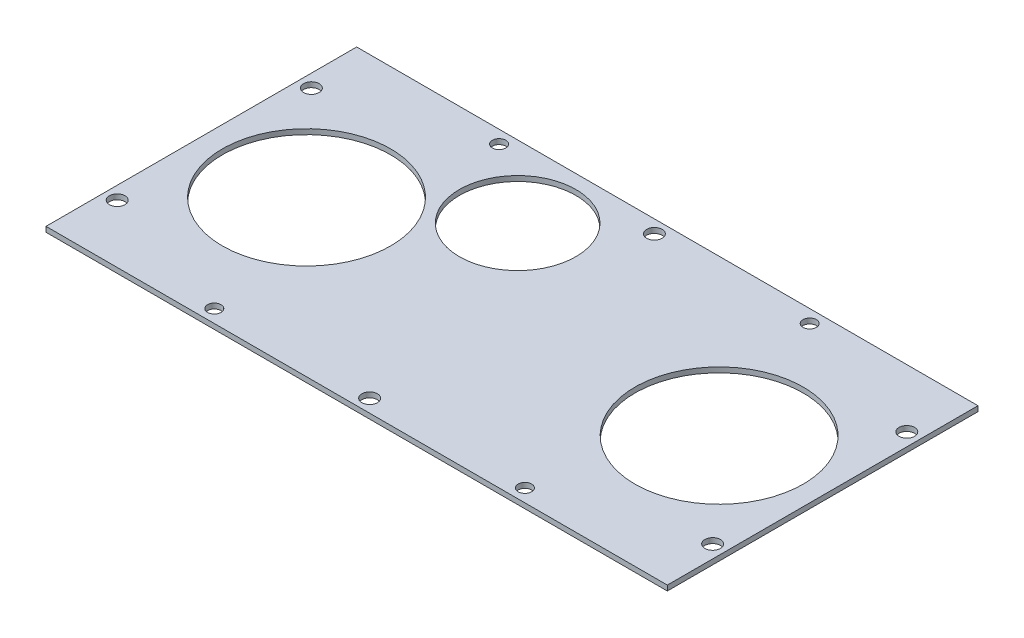
SolidWorks part; units mm, degrees
ref_plane "Front Plane" through (0, 0, 0) normal (0, 0, 1) x (1, 0, 0)
ref_plane "Top Plane" through (0, 0, 0) normal (0, 1, 0) x (1, 0, 0)
ref_plane "Right Plane" through (0, 0, 0) normal (1, 0, 0) x (0, 0, -1)
sketch "Sketch1" plane through (0, 0, 0) normal (0, 1, 0) x (1, 0, 0)
  line L1 (-152.4, 76.2) -> (152.4, 76.2)
  line L2 (-152.4, 76.2) -> (-152.4, -76.2)
  line L3 (-152.4, -76.2) -> (152.4, -76.2)
  line L4 (152.4, 76.2) -> (152.4, -76.2)
  circle A1 centre (-100.8031, 0) radius 41.275
  circle A2 centre (101.6, 0) radius 41.275
  circle A3 centre (146.05, 47.625) radius 3.81
  circle A4 centre (76.2, 69.85) radius 3.302
  circle A5 centre (-146.05, 47.625) radius 3.81
  circle A6 centre (-146.05, -47.625) radius 3.81
  circle A7 centre (-76.2, -69.85) radius 3.302
  circle A8 centre (76.2, -69.85) radius 3.302
  circle A9 centre (146.05, -47.625) radius 3.81
  circle A10 centre (0, -69.85) radius 3.81
  circle A11 centre (-76.2, 69.85) radius 3.302
  circle A12 centre (0, 69.85) radius 3.81
  dimension "D2" = 82.55
  dimension "D3" = 82.55
  dimension "D4" = 7.62
  dimension "D7" = 7.62
  dimension "D8" = 6.604
  dimension "D9" = 6.604
  dimension "D10" = 7.62
  dimension "D11" = 7.62
  dimension "D12" = 6.604
  dimension "D32" = 7.62
  dimension "D35" = 6.604
  dimension "D38" = 7.62
  dimension "D5" = 28.575
  dimension "D6" = 6.35
  dimension "D13" = 28.575
  dimension "D14" = 6.35
  dimension "D15" = 6.35
  dimension "D16" = 28.575
  dimension "D17" = 6.35
  dimension "D18" = 6.35
  dimension "D19" = 6.35
  dimension "D20" = 28.575
  dimension "D21" = 304.8
  dimension "D22" = 152.4
  dimension "D23" = 76.2
  dimension "D24" = 76.2
  dimension "D25" = 76.2
  dimension "D26" = 76.2
  dimension "D27" = 101.6
  dimension "D28" = 76.2
  dimension "D29" = 76.2
  dimension "D30" = 152.4
  dimension "D31" = 6.35
  dimension "D33" = 6.35
  dimension "D34" = 6.35
  dimension "D36" = 76.2
  dimension "D37" = 6.35
  dimension "D39" = 152.4
extrude "Boss-Extrude1" add sketch "Sketch1" along normal blind 2.54
sketch "Sketch2" plane through (0, 2.54, 0) normal (0, 1, 0) x (1, 0, 0)
  line L0 (152.4, 76.2) -> (-152.4, 76.2) construction
  line L1 (-152.4, 76.2) -> (-152.4, -76.2) construction
  circle A0 centre (-38.1, 40.8686) radius 28.575
  dimension "D1" = 57.15
  dimension "D2" = 35.3314
  dimension "D3" = 114.3
extrude "Cut-Extrude1" cut sketch "Sketch2" against normal through all
sketch "Sketch3" plane through (0, 2.54, 0) normal (0, 1, 0) x (1, 0, 0)
  line L0 (-137.345, -44.4484) -> (-61.145, -44.4484)
  line L1 (-146.5712, 73.7609) -> (-70.3712, 73.7609)
  line L2 (-146.5712, 73.7609) -> (-146.5712, 48.3609)
  line L3 (-146.5712, 48.3609) -> (-70.3712, 48.3609)
  line L4 (-70.3712, 73.7609) -> (-70.3712, 48.3609)
  line L5 (-52.792, 10.949) -> (48.808, 10.949)
  line L6 (-52.792, 10.949) -> (-52.792, -65.251)
  line L7 (-52.792, -65.251) -> (48.808, -65.251)
  line L8 (48.808, 10.949) -> (48.808, -65.251)
  line L9 (-137.345, -44.4484) -> (-137.345, -69.8484)
  line L10 (-137.345, -69.8484) -> (-61.145, -69.8484)
  line L11 (-61.145, -44.4484) -> (-61.145, -69.8484)
  line L12 (64.3363, -44.4484) -> (140.5363, -44.4484)
  line L13 (64.3363, -44.4484) -> (64.3363, -69.8484)
  line L14 (64.3363, -69.8484) -> (140.5363, -69.8484)
  line L15 (140.5363, -44.4484) -> (140.5363, -69.8484)
  line L16 (65.1876, 72.6941) -> (141.3876, 72.6941)
  line L17 (65.1876, 72.6941) -> (65.1876, 47.2941)
  line L18 (65.1876, 47.2941) -> (141.3876, 47.2941)
  line L19 (141.3876, 72.6941) -> (141.3876, 47.2941)
  line L21 (6.6258, 64.9038) -> (57.4258, 64.9038)
  line L22 (6.6258, 64.9038) -> (6.6258, 14.1038)
  line L23 (6.6258, 14.1038) -> (57.4258, 14.1038)
  line L24 (57.4258, 64.9038) -> (57.4258, 14.1038)
  dimension "D1" = 76.2
  dimension "D2" = 25.4
  dimension "D3" = 101.6
  dimension "D4" = 76.2
  dimension "D5" = 76.2
  dimension "D6" = 25.4
  dimension "D7" = 76.2
  dimension "D8" = 25.4
  dimension "D9" = 76.2
  dimension "D10" = 25.4
  dimension "D11" = 50.8
  dimension "D12" = 50.8
equation "\"D22@Sketch1\"=\"D21@Sketch1\"/2"
equation "\"D16@Sketch1\"=\"D13@Sketch1\""
equation "\"D5@Sketch1\"=\"D13@Sketch1\""
equation "\"D20@Sketch1\"=\"D13@Sketch1\""
equation "\"D19@Sketch1\"=\"D15@Sketch1\""
equation "\"D6@Sketch1\"=\"D14@Sketch1\""
equation "\"D17@Sketch1\"=\"D14@Sketch1\""
equation "\"D31@Sketch1\"=\"D17@Sketch1\""
equation "\"D18@Sketch1\"=\"D14@Sketch1\""
equation "\"D33@Sketch1\"=\"D14@Sketch1\""
equation "\"D34@Sketch1\"=\"D14@Sketch1\""
equation "\"D37@Sketch1\"=\"D34@Sketch1\""
equation "\"D10@Sketch1\"=\"D11@Sketch1\""
equation "\"D32@Sketch1\"=\"D10@Sketch1\""
equation "\"D38@Sketch1\"=\"D11@Sketch1\""
equation "\"D4@Sketch1\"=\"D38@Sketch1\""
equation "\"D7@Sketch1\"=\"D38@Sketch1\""
equation "\"D28@Sketch1\"=\"D39@Sketch1\"/2"
equation "\"D29@Sketch1\"=\"D28@Sketch1\""
equation "\"D26@Sketch1\"=\"D28@Sketch1\""
